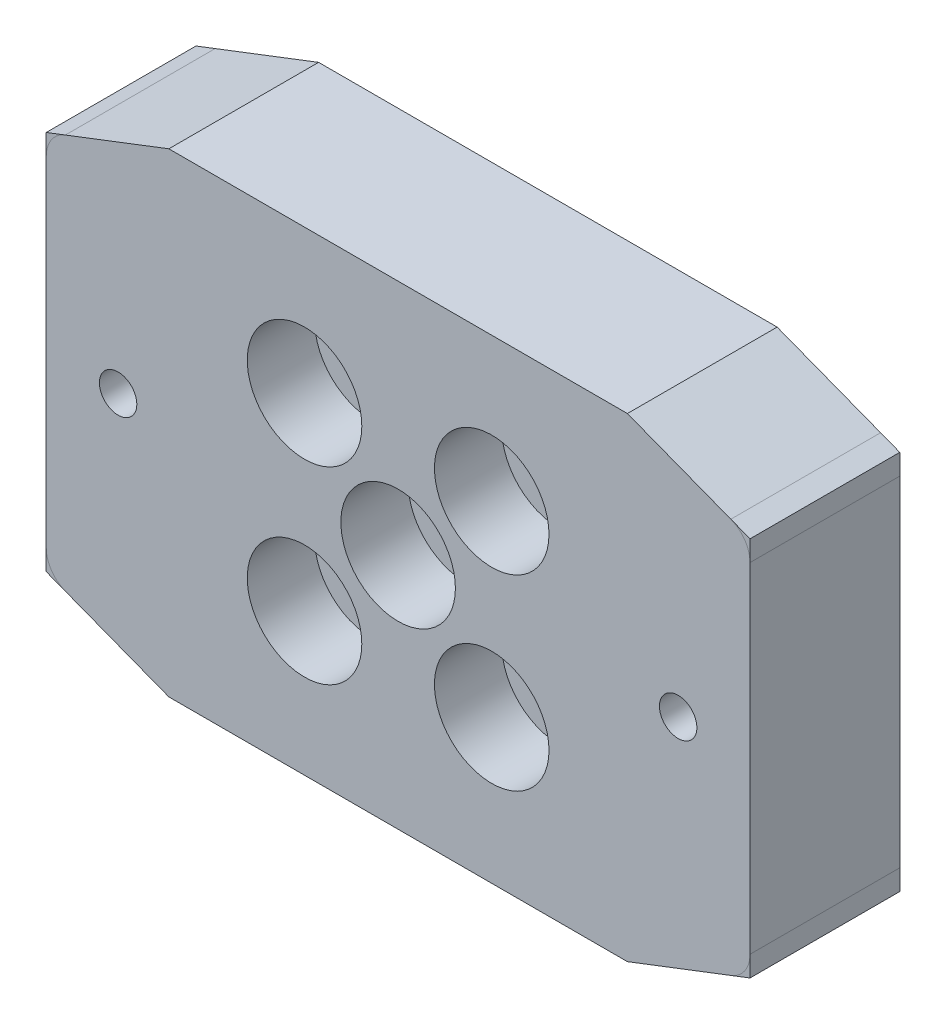
SolidWorks part; units mm, degrees
ref_plane "Front Plane" through (0, 0, 0) normal (0, 0, 1) x (1, 0, 0)
ref_plane "Top Plane" through (0, 0, 0) normal (0, 1, 0) x (1, 0, 0)
ref_plane "Right Plane" through (0, 0, 0) normal (1, 0, 0) x (0, 0, -1)
sketch "Sketch1" plane through (0, 0, 0) normal (0, 0, 1) x (1, 0, 0)
  line L0 (-48.6207, 0) -> (72.931, 0) construction
  line L1 (0, 34.4847) -> (0, -34.4847) construction
  line L2 (-12.7, 23.5) -> (12.7, 23.5)
  line L3 (-12.7, -23.5) -> (12.7, -23.5)
  line L4 (23.5, 12.7) -> (23.5, -12.7)
  line L5 (-23.5, 12.7) -> (-23.5, -12.7)
  line L10 (-23.5, 12.7) -> (-12.7, 23.5)
  line L11 (23.5, 12.7) -> (12.7, 23.5)
  line L12 (-23.5, -12.7) -> (-12.7, -23.5)
  line L13 (12.7, -23.5) -> (23.5, -12.7)
  circle A0 centre (0, 18.7) radius 1.25
  circle A1 centre (18.7, 0) radius 1.25
  circle A2 centre (0, -18.7) radius 1.25
  circle A3 centre (-18.7, 0) radius 1.25
  circle A4 centre (0, 0) radius 2.25
  circle A5 centre (-6.25, 6.25) radius 2.25
  circle A6 centre (6.25, 6.25) radius 2.25
  circle A7 centre (6.25, -6.25) radius 2.25
  circle A8 centre (-6.25, -6.35) radius 2.25
  dimension "D13" = 18.7
  dimension "D14" = 2.5
  dimension "D15" = 18.7
  dimension "D16" = 2.5
  dimension "D17" = 18.7
  dimension "D18" = 2.5
  dimension "D19" = 18.7
  dimension "D20" = 2.5
  dimension "D21" = 6.25
  dimension "D22" = 6.25
  dimension "D24" = 6.25
  dimension "D25" = 6.25
  dimension "D26" = 6.25
  dimension "D27" = 6.25
  dimension "D28" = 6.25
  dimension "D29" = 4.5
  dimension "D30" = 4.5
  dimension "D31" = 4.5
  dimension "D32" = 4.5
  dimension "D33" = 4.5
  dimension "D34" = 0
  dimension "D1" = 23.5
  dimension "D2" = 23.5
  dimension "D3" = 23.5
  dimension "D4" = 23.5
  dimension "D5" = 135
  dimension "D6" = 12.7
  dimension "D7" = 12.7
  dimension "D8" = 12.7
  dimension "D9" = 12.7
  dimension "D10" = 12.7
  dimension "D11" = 12.7
  dimension "D12" = 12.7
  dimension "6,25" = 6.35
extrude "Boss-Extrude1" add sketch "Sketch1" along normal blind 10
cosmetic thread "Cosmetic Thread1" parameters "D2"=3
cosmetic thread "Cosmetic Thread2" parameters "D2"=3
sketch "Sketch2" plane through (0, 0, 10) normal (0, 0, 1) x (1, 0, 0)
  circle A0 centre (-6.25, 6.25) radius 3.825
  circle A1 centre (6.25, 6.25) radius 3.825
  circle A2 centre (0, 0) radius 3.825
  circle A3 centre (-6.25, -6.35) radius 3.825
  circle A4 centre (6.25, -6.25) radius 3.825
  dimension "D1" = 7.65
  dimension "D2" = 7.65
  dimension "D3" = 7.65
  dimension "D4" = 7.65
  dimension "D5" = 7.65
extrude "Cut-Extrude1" cut sketch "Sketch2" against normal blind 4.5
sketch "Sketch3" plane through (0, 0, 10) normal (0, 0, 1) x (1, 0, 0)
  line L0 (-15.7, 15.7) -> (15.7, 15.7)
  line L1 (15.7, 15.7) -> (15.7, -15.7)
  line L2 (15.7, -15.7) -> (-15.7, -15.7)
  line L3 (-15.7, -15.7) -> (-15.7, 15.7)
  line L4 (-15.7, 15.7) -> (-12.7, 23.5)
  line L5 (-15.7, 15.7) -> (-23.5, 12.7)
  line L6 (12.7, 23.5) -> (15.7, 15.7)
  line L7 (23.5, 12.7) -> (12.7, 23.5) construction
  line L8 (23.5, 12.7) -> (15.7, 15.7)
  line L9 (15.7, 15.7) -> (15.6402, 15.9195)
  line L10 (23.5, -12.7) -> (15.7, -15.7)
  line L11 (15.7, -15.7) -> (12.7, -23.5)
  line L12 (-23.5, -12.7) -> (-15.7, -15.7)
  line L13 (-15.7, -15.7) -> (-12.7, -23.5)
  line L14 (12.7, -23.5) -> (23.5, -12.7) construction
  line L15 (-23.5, -12.7) -> (-12.7, -23.5) construction
  line L16 (-12.7, 23.5) -> (-23.5, 12.7) construction
  line L17 (23.5, 12.7) -> (12.7, 23.5)
  line L18 (12.7, -23.5) -> (23.5, -12.7)
  line L19 (-23.5, -12.7) -> (-12.7, -23.5)
  line L20 (-12.7, 23.5) -> (-23.5, 12.7)
  dimension "D1" = 15.7
  dimension "D2" = 15.7
  dimension "D3" = 15.7
  dimension "D4" = 15.7
extrude "Cut-Extrude2" cut sketch "Sketch3" against normal blind 10
fillet "Fillet1" radius 2 12 edges at (-15.7, -15.7, 5) (15.7, -15.7, 5) (15.7, 15.7, 5) (-15.7, 15.7, 5) (-23.5, 12.7, 5) (-12.7, 23.5, 5) (12.7, 23.5, 5) (23.5, 12.7, 5) (-23.5, -12.7, 5) (23.5, -12.7, 5) (-12.7, -23.5, 5) (12.7, -23.5, 5)
sketch "Sketch5" plane through (0, 0, 10) normal (0, 0, 1) x (1, 0, 0)
  line L0 (-31.7917, 0) -> (32.1702, 0) construction
  line L1 (-15.7883, 15.88) -> (15.7883, 15.88)
  line L2 (-15.7883, -15.88) -> (15.7883, -15.88)
  line L3 (15.3809, -16.5296) -> (13.1931, -22.218) construction
  line L4 (-11.3264, -23.5) -> (11.3264, -23.5) construction
  line L5 (-15.3809, -16.5296) -> (-13.1931, -22.218) construction
  line L6 (13.1931, 22.218) -> (15.3809, 16.5296) construction
  line L7 (11.3264, 23.5) -> (-11.3264, 23.5) construction
  line L8 (-15.3809, 16.5296) -> (-13.1931, 22.218) construction
  line L9 (15.3809, -16.5296) -> (13.1931, -22.218)
  line L10 (-11.3264, -23.5) -> (11.3264, -23.5)
  line L11 (-15.3809, -16.5296) -> (-13.1931, -22.218)
  line L12 (13.1931, 22.218) -> (15.3809, 16.5296)
  line L13 (11.3264, 23.5) -> (-11.3264, 23.5)
  line L14 (-15.3809, 16.5296) -> (-13.1931, 22.218)
  arc A0 (16.5296, -15.3809) -> (15.3809, -16.5296) centre (17.2476, -17.2476) ccw construction
  arc A1 (11.3264, -23.5) -> (13.1931, -22.218) centre (11.3264, -21.5) ccw construction
  arc A2 (-13.1931, -22.218) -> (-11.3264, -23.5) centre (-11.3264, -21.5) ccw construction
  arc A3 (-15.3809, -16.5296) -> (-16.5296, -15.3809) centre (-17.2476, -17.2476) ccw construction
  arc A4 (-16.5296, 15.3809) -> (-15.3809, 16.5296) centre (-17.2476, 17.2476) ccw construction
  arc A5 (15.3809, 16.5296) -> (16.5296, 15.3809) centre (17.2476, 17.2476) ccw construction
  arc A6 (13.1931, 22.218) -> (11.3264, 23.5) centre (11.3264, 21.5) ccw construction
  arc A7 (-11.3264, 23.5) -> (-13.1931, 22.218) centre (-11.3264, 21.5) ccw construction
  arc A8 (15.7883, -15.88) -> (15.3809, -16.5296) centre (17.2476, -17.2476) ccw
  arc A9 (11.3264, -23.5) -> (13.1931, -22.218) centre (11.3264, -21.5) ccw
  arc A10 (-13.1931, -22.218) -> (-11.3264, -23.5) centre (-11.3264, -21.5) ccw
  arc A11 (-15.3809, -16.5296) -> (-15.7883, -15.88) centre (-17.2476, -17.2476) ccw
  arc A12 (-15.7883, 15.88) -> (-15.3809, 16.5296) centre (-17.2476, 17.2476) ccw
  arc A13 (15.3809, 16.5296) -> (15.7883, 15.88) centre (17.2476, 17.2476) ccw
  arc A14 (13.1931, 22.218) -> (11.3264, 23.5) centre (11.3264, 21.5) ccw
  arc A15 (-11.3264, 23.5) -> (-13.1931, 22.218) centre (-11.3264, 21.5) ccw
  dimension "D1" = 15.88
  dimension "D2" = 15.88
extrude "Cut-Extrude3" cut sketch "Sketch5" against normal blind 10
sketch "Sketch6" plane through (0, 0, 10) normal (0, 0, 1) x (1, 0, 0)
  line L0 (-22.218, -13.1931) -> (-16.5296, -15.3809) construction
  line L1 (15.7883, -15.88) -> (-15.7883, -15.88) construction
  line L2 (22.218, -13.1931) -> (16.5296, -15.3809) construction
  line L3 (22.218, 13.1931) -> (16.5296, 15.3809) construction
  line L4 (-15.7883, 15.88) -> (15.7883, 15.88) construction
  line L5 (-16.5296, 15.3809) -> (-22.218, 13.1931) construction
  line L6 (-16.5296, -15.3809) -> (-15.232, -15.88)
  line L7 (15.7883, -15.88) -> (15.232, -15.88)
  line L8 (16.5296, -15.3809) -> (15.232, -15.88)
  line L9 (16.5296, 15.3809) -> (15.232, 15.88)
  line L10 (-15.7883, 15.88) -> (-15.232, 15.88)
  line L11 (-15.232, 15.88) -> (-16.5296, 15.3809)
  line L12 (-15.232, -15.88) -> (-15.7883, -15.88)
  line L13 (15.232, 15.88) -> (15.7883, 15.88)
  arc A0 (-15.7883, -15.88) -> (-16.5296, -15.3809) centre (-17.2476, -17.2476) ccw construction
  arc A1 (16.5296, -15.3809) -> (15.7883, -15.88) centre (17.2476, -17.2476) ccw construction
  arc A2 (15.7883, 15.88) -> (16.5296, 15.3809) centre (17.2476, 17.2476) ccw construction
  arc A3 (-16.5296, 15.3809) -> (-15.7883, 15.88) centre (-17.2476, 17.2476) ccw construction
  arc A4 (-15.7883, -15.88) -> (-16.5296, -15.3809) centre (-17.2476, -17.2476) ccw
  arc A5 (16.5296, -15.3809) -> (15.7883, -15.88) centre (17.2476, -17.2476) ccw
  arc A6 (15.7883, 15.88) -> (16.5296, 15.3809) centre (17.2476, 17.2476) ccw
  arc A7 (-16.5296, 15.3809) -> (-15.7883, 15.88) centre (-17.2476, 17.2476) ccw
extrude "Cut-Extrude4" cut sketch "Sketch6" against normal blind 10 contours L10 L11 A7 | L9 L13 A6 | L8 L7 A5 | L6 L12 A4
sketch "Sketch7" plane through (0, 0, 10) normal (0, 0, 1) x (1, 0, 0)
  line L0 (-15.31, 15.85) -> (15.31, 15.85)
  line L1 (-15.31, -15.85) -> (15.31, -15.85)
  line L2 (15.232, -15.88) -> (-15.232, -15.88) construction
  line L3 (-15.232, 15.88) -> (15.232, 15.88) construction
  line L4 (-22.218, -13.1931) -> (-15.232, -15.88) construction
  line L5 (22.218, -13.1931) -> (15.232, -15.88) construction
  line L6 (-15.232, 15.88) -> (-22.218, 13.1931) construction
  line L7 (22.218, 13.1931) -> (15.232, 15.88) construction
  line L8 (15.232, -15.88) -> (-15.232, -15.88)
  line L9 (-15.31, -15.85) -> (-15.232, -15.88)
  line L10 (15.31, -15.85) -> (15.232, -15.88)
  line L11 (-15.232, 15.88) -> (-15.31, 15.85)
  line L12 (15.31, 15.85) -> (15.232, 15.88)
  line L13 (-15.232, 15.88) -> (15.232, 15.88)
  dimension "D1" = 0.03
  dimension "D2" = 0.03
extrude "Cut-Extrude6" cut sketch "Sketch7" against normal blind 10
sketch "Sketch8" plane through (0, 0, 10) normal (0, 0, 1) x (1, 0, 0)
  line L0 (-23.5, -11.3264) -> (-23.5, -12.7)
  line L1 (23.5, 11.3264) -> (23.5, 12.7)
  line L8 (15.31, 15.85) -> (-15.31, 15.85)
  line L9 (-15.31, 15.85) -> (-22.218, 13.1931)
  line L10 (-23.5, 11.3264) -> (-23.5, -11.3264)
  line L11 (-22.218, -13.1931) -> (-15.31, -15.85)
  line L12 (-15.31, -15.85) -> (15.31, -15.85)
  line L13 (15.31, -15.85) -> (22.218, -13.1931)
  line L14 (23.5, -11.3264) -> (23.5, 11.3264)
  line L15 (22.218, 13.1931) -> (15.31, 15.85)
  line L17 (-22.218, 13.1931) -> (-23.5, 12.7)
  line L18 (-23.5, 12.7) -> (-23.5, 11.3264)
  line L19 (-23.5, -12.7) -> (-22.218, -13.1931)
  line L21 (22.218, -13.1931) -> (23.5, -12.7)
  line L22 (23.5, -12.7) -> (23.5, -11.3264)
  line L23 (23.5, 12.7) -> (22.218, 13.1931)
  arc A4 (-22.218, 13.1931) -> (-23.5, 11.3264) centre (-21.5, 11.3264) ccw
  arc A5 (-23.5, -11.3264) -> (-22.218, -13.1931) centre (-21.5, -11.3264) ccw
  arc A6 (22.218, -13.1931) -> (23.5, -11.3264) centre (21.5, -11.3264) ccw
  arc A7 (23.5, 11.3264) -> (22.218, 13.1931) centre (21.5, 11.3264) ccw
  arc A8 (-22.218, 13.1931) -> (-23.5, 11.3264) centre (-21.5, 11.3264) ccw
  arc A9 (-23.5, -11.3264) -> (-22.218, -13.1931) centre (-21.5, -11.3264) ccw
  arc A10 (22.218, -13.1931) -> (23.5, -11.3264) centre (21.5, -11.3264) ccw
  arc A11 (23.5, 11.3264) -> (22.218, 13.1931) centre (21.5, 11.3264) ccw
  dimension "D1" = 0
extrude "Boss-Extrude2" add sketch "Sketch8" against normal up to surface (10 mm away) separate body up to face at (19.95, 0, 0)
